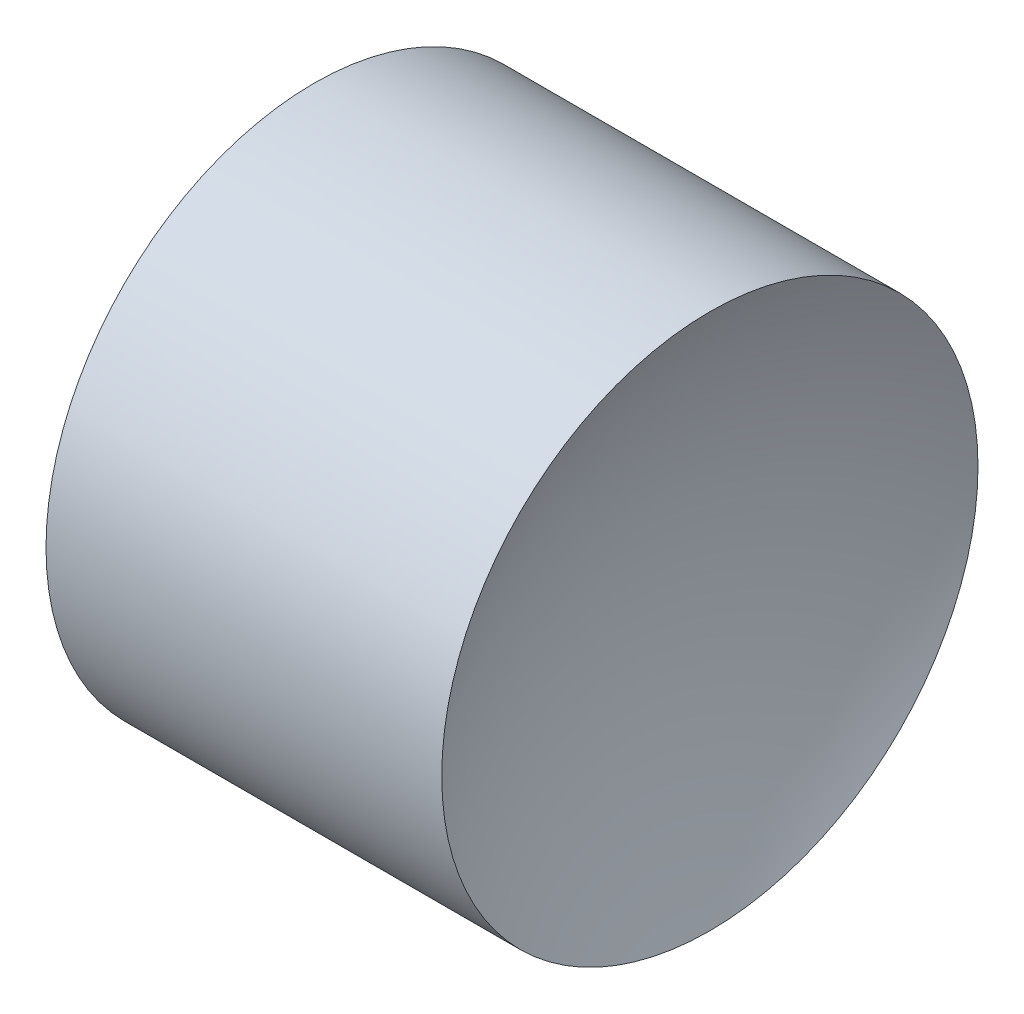
SolidWorks part; units mm, degrees
ref_plane "前视基准面" through (0, 0, 0) normal (0, 0, 1) x (1, 0, 0)
ref_plane "上视基准面" through (0, 0, 0) normal (0, 1, 0) x (1, 0, 0)
ref_plane "右视基准面" through (0, 0, 0) normal (1, 0, 0) x (0, 0, -1)
sketch "草图1" plane through (0, 0, 0) normal (0, 0, 1) x (1, 0, 0)
  line L0 (5.3062, 3.2611) -> (6.9581, 3.2611) construction
  line L1 (6.4896, 3.2611) -> (5.4896, 3.2611)
  line L3 (5.9896, 4.2611) -> (6.7276, 4.2611)
  line L4 (5.9896, 4.2611) -> (5.2516, 4.2611)
  arc A0 (5.4896, 3.2611) -> (5.2516, 4.2611) centre (3.2696, 3.2611) ccw
  arc A1 (6.7276, 4.2611) -> (6.4896, 3.2611) centre (8.7096, 3.2611) ccw
  dimension "D1" = 2.22
  dimension "D2" = 2.22
  dimension "D3" = 1.476
  dimension "D4" = 1
revolve "旋转1" add sketch "草图1" angle 360 about L0
